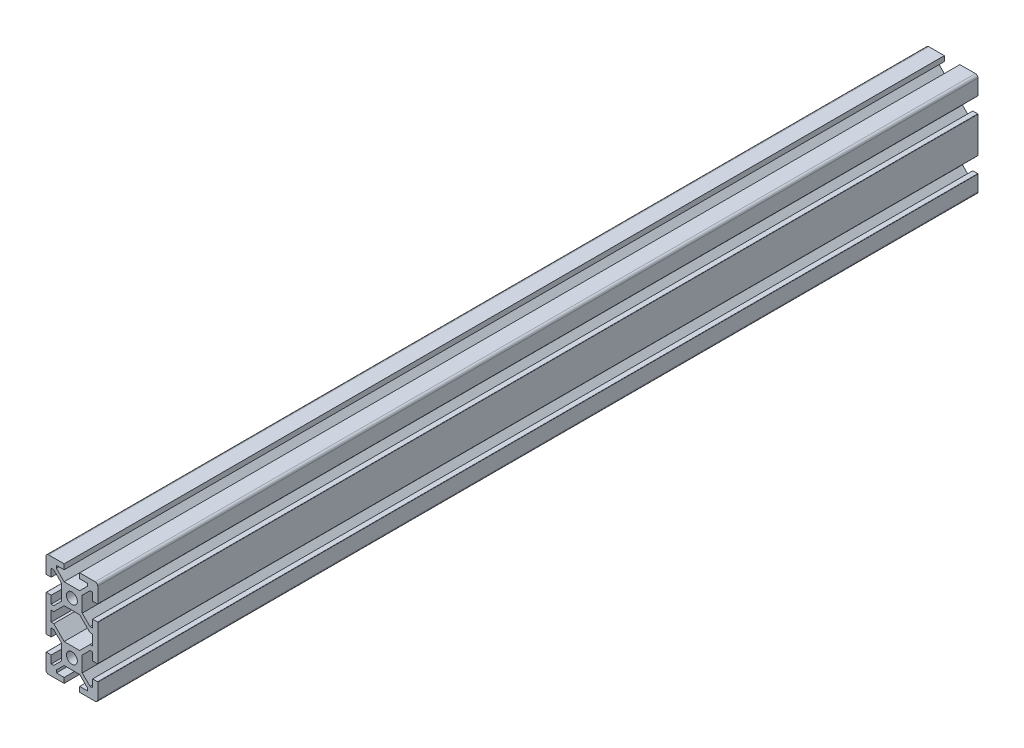
SolidWorks part; units mm, degrees
ref_plane "Front Plane" through (0, 0, 0) normal (0, 0, 1) x (1, 0, 0)
ref_plane "Top Plane" through (0, 0, 0) normal (0, 1, 0) x (1, 0, 0)
ref_plane "Right Plane" through (0, 0, 0) normal (1, 0, 0) x (0, 0, -1)
sketch "Sketch1" plane through (0, 0, 0) normal (0, 0, 1) x (1, 0, 0)
  line L0 (-7, -2) -> (-8, -2)
  line L1 (-8, -2) -> (-8, 2)
  line L2 (-8, 2) -> (-7, 2)
  line L3 (-7, 2) -> (-3, 6)
  line L4 (-3, 6) -> (3, 6)
  line L5 (3, 6) -> (7, 2)
  line L6 (7, 2) -> (8, 2)
  line L7 (8, 2) -> (8, -2)
  line L8 (8, -2) -> (7, -2)
  line L9 (7, -2) -> (3, -6)
  line L10 (3, -6) -> (-3, -6)
  line L11 (-3, -6) -> (-7, -2)
  line L12 (10, -19) -> (10, -13)
  line L13 (10, -13) -> (8, -13)
  line L14 (8, -13) -> (8, -16)
  line L15 (8, -16) -> (7, -16)
  line L16 (7, -16) -> (4, -13)
  line L17 (4, -13) -> (4, -7)
  line L18 (4, -7) -> (7, -4)
  line L19 (7, -4) -> (8, -4)
  line L20 (8, -4) -> (8, -7)
  line L21 (8, -7) -> (10, -7)
  line L22 (10, -7) -> (10, 7)
  line L23 (10, 7) -> (8, 7)
  line L24 (8, 7) -> (8, 4)
  line L25 (8, 4) -> (7, 4)
  line L26 (7, 4) -> (4, 7)
  line L27 (4, 7) -> (4, 13)
  line L28 (4, 13) -> (7, 16)
  line L29 (7, 16) -> (8, 16)
  line L30 (8, 16) -> (8, 13)
  line L31 (8, 13) -> (10, 13)
  line L32 (10, 13) -> (10, 19)
  line L33 (9, 20) -> (3, 20)
  line L34 (3, 20) -> (3, 18)
  line L35 (3, 18) -> (6, 18)
  line L36 (6, 18) -> (6, 17)
  line L37 (6, 17) -> (3, 14)
  line L38 (3, 14) -> (-3, 14)
  line L39 (-3, 14) -> (-6, 17)
  line L40 (-6, 17) -> (-6, 18)
  line L41 (-6, 18) -> (-3, 18)
  line L42 (-3, 18) -> (-3, 20)
  line L43 (-3, 20) -> (-9, 20)
  line L44 (-10, 19) -> (-10, 13)
  line L45 (-10, 13) -> (-8, 13)
  line L46 (-8, 13) -> (-8, 16)
  line L47 (-8, 16) -> (-7, 16)
  line L48 (-7, 16) -> (-4, 13)
  line L49 (-4, 13) -> (-4, 7)
  line L50 (-4, 7) -> (-7, 4)
  line L51 (-7, 4) -> (-8, 4)
  line L52 (-8, 4) -> (-8, 7)
  line L53 (-8, 7) -> (-10, 7)
  line L54 (-10, 7) -> (-10, -7)
  line L55 (-10, -7) -> (-8, -7)
  line L56 (-8, -7) -> (-8, -4)
  line L57 (-8, -4) -> (-7, -4)
  line L58 (-7, -4) -> (-4, -7)
  line L59 (-4, -7) -> (-4, -13)
  line L60 (-4, -13) -> (-7, -16)
  line L61 (-7, -16) -> (-8, -16)
  line L62 (-8, -16) -> (-8, -13)
  line L63 (-8, -13) -> (-10, -13)
  line L64 (-10, -13) -> (-10, -19)
  line L65 (-9, -20) -> (-3, -20)
  line L66 (-3, -20) -> (-3, -18)
  line L67 (-3, -18) -> (-6, -18)
  line L68 (-6, -18) -> (-6, -17)
  line L69 (-6, -17) -> (-3, -14)
  line L70 (-3, -14) -> (3, -14)
  line L71 (3, -14) -> (6, -17)
  line L72 (6, -17) -> (6, -18)
  line L73 (6, -18) -> (3, -18)
  line L74 (3, -18) -> (3, -20)
  line L75 (3, -20) -> (9, -20)
  line L76 (-8, 0) -> (0, 0) construction
  line L77 (0, 0) -> (8, 0) construction
  line L78 (0, 6) -> (0, 0) construction
  line L79 (0, 0) -> (0, -6) construction
  circle A0 centre (0, -10) radius 2.1
  circle A1 centre (0, 10) radius 2.1
  arc A2 (9, -20) -> (10, -19) centre (9, -19) ccw
  arc A3 (10, 19) -> (9, 20) centre (9, 19) ccw
  arc A4 (-9, 20) -> (-10, 19) centre (-9, 19) ccw
  arc A5 (-10, -19) -> (-9, -20) centre (-9, -19) ccw
  dimension "D1" = 40
  dimension "D2" = 20
extrude "Boss-Extrude1" add sketch "Sketch1" against normal blind 340
fillet "Fillet1" radius 0.1 8 edges at (10, -13, -170) (10, -7, -170) (10, 7, -170) (10, 13, -170) (-10, 13, -170) (-10, -13, -170) (-10, -7, -170) (-10, 7, -170)
